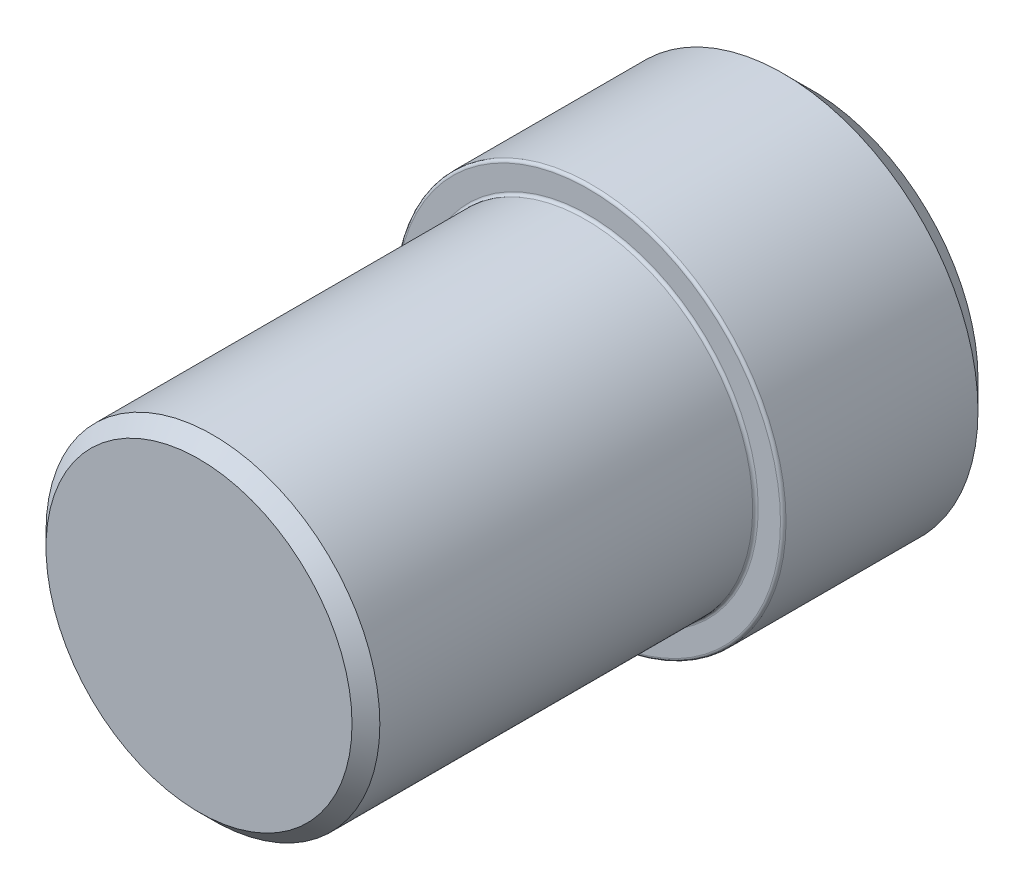
SolidWorks part; units mm, degrees
ref_plane "Piano frontale" through (0, 0, 0) normal (0, 0, 1) x (1, 0, 0)
ref_plane "Piano superiore" through (0, 0, 0) normal (0, 1, 0) x (1, 0, 0)
ref_plane "Piano destro" through (0, 0, 0) normal (1, 0, 0) x (0, 0, -1)
sketch "Schizzo1" plane through (0, 0, 0) normal (0, 0, 1) x (1, 0, 0)
  circle A0 centre (0, 0) radius 3.5
  dimension "D1" = 7
extrude "Estrusione-Estrusione1" add sketch "Schizzo1" along normal blind 4
sketch "Schizzo2" plane through (0, 0, 4) normal (0, 0, 1) x (1, 0, 0)
  circle A0 centre (0, 0) radius 3
  dimension "D1" = 6
extrude "Estrusione-Estrusione2" add sketch "Schizzo2" along normal blind 7
chamfer "Smusso1" distance 0.25 angle 45 1 edges at (3, 0, 11)
chamfer "Smusso2" distance 0.5 angle 45 1 edges at (3.5, 0, 0)
fillet "Raccordo1" radius 0.05 2 edges at (3.5, 0, 4) (3, 0, 4)
